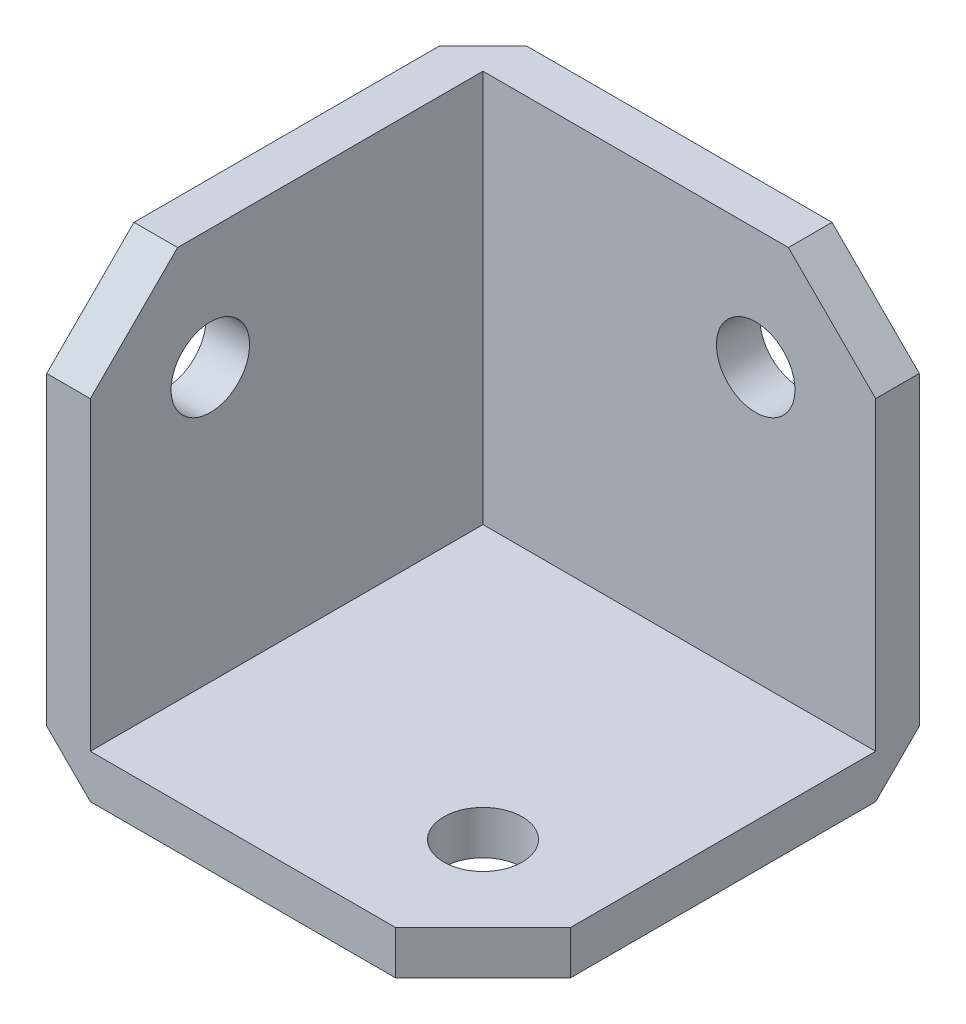
SolidWorks part; units mm, degrees
ref_plane "Front Plane" through (0, 0, 0) normal (0, 0, 1) x (1, 0, 0)
ref_plane "Top Plane" through (0, 0, 0) normal (0, 1, 0) x (1, 0, 0)
ref_plane "Right Plane" through (0, 0, 0) normal (1, 0, 0) x (0, 0, -1)
sketch "Sketch2" plane through (0, 0, 0) normal (0, 0, 1) x (1, 0, 0)
  line L1 (0, 0) -> (25.4, 0)
  line L2 (0, 0) -> (0, 25.4)
  line L3 (0, 25.4) -> (25.4, 25.4)
  line L4 (25.4, 0) -> (25.4, 25.4)
  dimension "D1" = 25.4
  dimension "D2" = 25.4
extrude "Boss-Extrude2" add sketch "Sketch2" along normal blind 25.4
sketch "Sketch3" plane through (0, 0, 25.4) normal (0, 0, 1) x (1, 0, 0)
  line L0 (0, 0) -> (25.4, 0) construction
  line L1 (25.4, 25.4) -> (2.54, 25.4)
  line L2 (25.4, 25.4) -> (25.4, 2.54)
  line L3 (25.4, 2.54) -> (2.54, 2.54)
  line L4 (2.54, 25.4) -> (2.54, 2.54)
  line L5 (0, 25.4) -> (0, 0) construction
  dimension "D1" = 2.54
  dimension "D2" = 2.54
extrude "Cut-Extrude1" cut sketch "Sketch3" against normal blind 22.86
sketch "Sketch4" plane through (0, 0, 2.54) normal (0, 0, 1) x (1, 0, 0)
  line L1 (2.54, 25.4) -> (2.54, 2.54) construction
  line L2 (2.54, 2.54) -> (25.4, 2.54) construction
  circle A0 centre (18.415, 18.415) radius 2.286
  dimension "D1" = 4.572
  dimension "D2" = 15.875
  dimension "D3" = 15.875
extrude "Cut-Extrude3" cut sketch "Sketch4" against normal blind 2.54
sketch "Sketch5" plane through (2.54, 0, 0) normal (1, 0, 0) x (0, 0, -1)
  line L0 (-2.54, 2.54) -> (-2.54, 25.4) construction
  line L1 (-2.54, 2.54) -> (-25.4, 2.54) construction
  circle A0 centre (-18.415, 18.415) radius 2.286
  dimension "D1" = 4.572
  dimension "D2" = 15.875
  dimension "D3" = 15.875
extrude "Cut-Extrude4" cut sketch "Sketch5" against normal blind 2.54
sketch "Sketch6" plane through (0, 2.54, 0) normal (0, 1, 0) x (1, 0, 0)
  line L0 (2.54, -2.54) -> (25.4, -2.54) construction
  line L1 (2.54, -2.54) -> (2.54, -25.4) construction
  circle A0 centre (18.415, -18.415) radius 2.286
  dimension "D1" = 4.572
  dimension "D2" = 15.875
  dimension "D3" = 15.875
extrude "Cut-Extrude5" cut sketch "Sketch6" against normal blind 2.54
chamfer "Chamfer1" distance 5.08 angle 45 3 edges at (25.4, 1.27, 25.4) (25.4, 25.4, 1.27) (1.27, 25.4, 25.4)
chamfer "Chamfer2" distance 2.54 angle 45 3 edges at (0, 0, 12.7) (0, 12.7, 0) (12.7, 0, 0)
